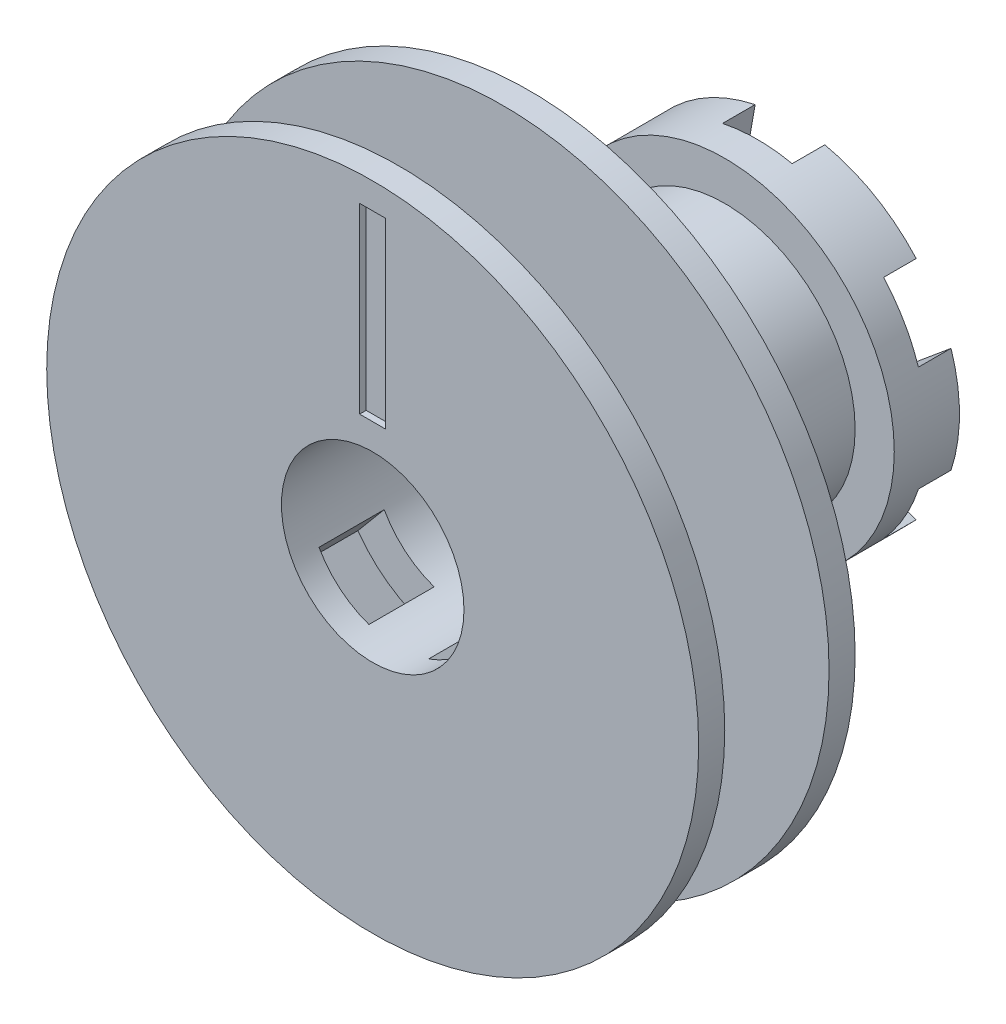
SolidWorks part; units mm, degrees
ref_plane "正面(Front)" through (0, 0, 0) normal (0, 0, 1) x (1, 0, 0)
ref_plane "平面(Top)" through (0, 0, 0) normal (0, 1, 0) x (1, 0, 0)
ref_plane "右側面(Right)" through (0, 0, 0) normal (1, 0, 0) x (0, 0, -1)
sketch "ｽｹｯﾁ1" plane through (0, 0, 0) normal (0, 0, 1) x (1, 0, 0)
  line L0 (0, 0) -> (0, 32.0386) construction
  line L1 (3.75, 6.4952) -> (2.4634, 13.9265)
  line L2 (0, 0) -> (3.75, 6.4952) construction
  arc A0 (2.4634, 13.9265) -> (0, 16) centre (0, 13.5) ccw
  dimension "D1" = 2.5
  dimension "D2" = 7.5
  dimension "D3" = 30
  dimension "D4" = 16
sketch "ｽｹｯﾁ2" plane through (0, 0, 0) normal (0, 0, 1) x (1, 0, 0)
  line L0 (3.75, 6.4952) -> (2.4634, 13.9265) construction
  line L1 (3.75, 6.4952) -> (2.4634, 13.9265)
  line L3 (0, 0) -> (0, 32.0386) construction
  line L4 (0, 0) -> (0, 32.0386) construction
  line L5 (-3.75, 6.4952) -> (-2.4634, 13.9265)
  line L6 (7.5, 0) -> (13.2924, 4.8299)
  line L7 (3.75, 6.4952) -> (10.829, 9.0966)
  line L8 (3.75, -6.4952) -> (10.829, -9.0966)
  line L9 (7.5, 0) -> (13.2924, -4.8299)
  line L10 (-3.75, -6.4952) -> (-2.4634, -13.9265)
  line L11 (3.75, -6.4952) -> (2.4634, -13.9265)
  line L12 (-7.5, 0) -> (-13.2924, -4.8299)
  line L13 (-3.75, -6.4952) -> (-10.829, -9.0966)
  line L14 (-3.75, 6.4952) -> (-10.829, 9.0966)
  line L15 (-7.5, 0) -> (-13.2924, 4.8299)
  line L16 (0, 0) -> (3.75, 6.4952) construction
  arc A0 (2.4634, 13.9265) -> (0, 16) centre (0, 13.5) ccw construction
  arc A1 (2.4634, 13.9265) -> (-2.4634, 13.9265) centre (0, 13.5) ccw
  arc A2 (13.2924, 4.8299) -> (10.829, 9.0966) centre (11.6913, 6.75) ccw
  arc A3 (10.829, -9.0966) -> (13.2924, -4.8299) centre (11.6913, -6.75) ccw
  arc A4 (-2.4634, -13.9265) -> (2.4634, -13.9265) centre (0, -13.5) ccw
  arc A5 (-13.2924, -4.8299) -> (-10.829, -9.0966) centre (-11.6913, -6.75) ccw
  arc A6 (-10.829, 9.0966) -> (-13.2924, 4.8299) centre (-11.6913, 6.75) ccw
  dimension "D2" = 7.5
  dimension "D3" = 30
  dimension "D1" = 6
sketch "ｽｹｯﾁ3" plane through (0, 0, 0) normal (0, 0, 1) x (1, 0, 0)
  circle A0 centre (0, 0) radius 13
  dimension "D1" = 26
extrude "ﾎﾞｽ - 押し出し1" add sketch "ｽｹｯﾁ3" along normal blind 5
extrude "ｶｯﾄ - 押し出し2" cut sketch "ｽｹｯﾁ2" along normal blind 2.5
sketch "ｽｹｯﾁ4" plane through (0, 0, 5) normal (0, 0, 1) x (1, 0, 0)
  circle A0 centre (0, 0) radius 10
  dimension "D1" = 20
sketch "ｽｹｯﾁ11" plane through (0, 0, 5) normal (0, 0, 1) x (1, 0, 0)
  circle A0 centre (0, 0) radius 10
  dimension "D1" = 20
extrude "ﾎﾞｽ - 押し出し2" add sketch "ｽｹｯﾁ11" along normal blind 15
sketch "ｽｹｯﾁ5" plane through (0, 0, 0) normal (0, 1, 0) x (1, 0, 0)
  line L0 (0, 0) -> (0, -21.9976) construction
  line L1 (0, -20) -> (25, -20)
  line L2 (-10, -20) -> (10, -20) construction
  line L3 (25, -20) -> (25, -22)
  line L4 (25, -22) -> (10, -22)
  line L5 (10, -22) -> (10, -30)
  line L6 (10, -30) -> (25, -30)
  line L7 (25, -30) -> (25, -32)
  line L8 (25, -32) -> (0, -32)
  line L9 (0, -20) -> (0, -32)
  dimension "D1" = 2
  dimension "D2" = 2
  dimension "D3" = 8
  dimension "D4" = 10
  dimension "D5" = 25
revolve "回転1" add sketch "ｽｹｯﾁ5" angle 360 about L0
sketch "ｽｹｯﾁ6" plane through (0, 0, 32) normal (0, 0, 1) x (1, 0, 0)
  circle A0 centre (0, 0) radius 2
  dimension "D1" = 4
extrude "ｶｯﾄ - 押し出し3" cut sketch "ｽｹｯﾁ6" against normal through all
sketch "ｽｹｯﾁ7" plane through (0, 0, 32) normal (0, 0, 1) x (1, 0, 0)
  circle A0 centre (0, 0) radius 7
  dimension "D1" = 14
extrude "ｶｯﾄ - 押し出し4" cut sketch "ｽｹｯﾁ7" against normal blind 23
sketch "ｽｹｯﾁ8" plane through (0, 0, 32) normal (0, 0, 1) x (1, 0, 0)
  line L0 (14.7902, 2.5) -> (9.6825, 2.5)
  line L1 (12.9904, 7.5) -> (6.6144, 7.5)
  line L2 (0, 0) -> (27.9307, 0) construction
  line L3 (14.7902, -2.5) -> (9.6825, -2.5)
  line L4 (12.9904, -7.5) -> (6.6144, -7.5)
  circle A0 centre (0, 0) radius 10 construction
  arc A1 (14.7902, 2.5) -> (12.9904, 7.5) centre (0, 0) ccw
  arc A2 (9.6825, 2.5) -> (6.6144, 7.5) centre (0, 0) ccw
  arc A3 (9.6825, -2.5) -> (6.6144, -7.5) centre (0, 0) cw
  arc A4 (14.7902, -2.5) -> (12.9904, -7.5) centre (0, 0) cw
  dimension "D1" = 20
  dimension "D4" = 5
  dimension "D2" = 5
  dimension "D3" = 5
extrude "ｶｯﾄ - 押し出し5" [suppressed] cut sketch "ｽｹｯﾁ8" against normal up to next contours A4 L3 A3 L4 | A2 L0 A1 L1
sketch "ｽｹｯﾁ9" plane through (0, 0, 30) normal (0, 0, -1) x (-1, 0, 0)
  line L0 (0, 0) -> (-20.5505, -24.4911) construction
  line L1 (0, 0) -> (0, -32.4809) construction
  line L2 (-3.8435, -0.6912) -> (-11.5569, -9.8837)
  line L3 (-3.8435, -0.6912) -> (-0.0133, -3.9051)
  line L4 (-11.5569, -9.8837) -> (-7.7267, -13.0976)
  line L5 (-0.0133, -3.9051) -> (-7.7267, -13.0976)
  line L6 (-3.8435, -0.6912) -> (-7.7267, -13.0976) construction
  line L7 (-11.5569, -9.8837) -> (-0.0133, -3.9051) construction
  point P5 (-5.7851, -6.8944)
  dimension "D1" = 40
  dimension "D2" = 5
  dimension "D3" = 12
  dimension "D4" = 3
extrude "ｶｯﾄ - 押し出し6" cut sketch "ｽｹｯﾁ9" along normal blind 5
mirror "ﾐﾗｰ1" about plane through (0, 0, 0) normal (1, 0, 0) of "ｶｯﾄ - 押し出し6"
fillet "ﾌｨﾚｯﾄ1" radius 1 2 edges at (4.3087, -9.0242, 27.5) (-4.3087, -9.0242, 27.5)
sketch "ｽｹｯﾁ10" plane through (0, 0, 32) normal (0, 0, 1) x (1, 0, 0)
  line L0 (0, 0) -> (0, 32.0386) construction
  line L1 (-1, 23) -> (1, 23)
  line L2 (-1, 23) -> (-1, 9)
  line L3 (-1, 9) -> (1, 9)
  line L4 (1, 23) -> (1, 9)
  line L5 (-1, 23) -> (1, 9) construction
  line L6 (-1, 9) -> (1, 23) construction
  circle A0 centre (0, 0) radius 25 construction
  circle A2 centre (0, 0) radius 7 construction
  point P0 (0, 16)
  dimension "D1" = 2
  dimension "D2" = 2
  dimension "D3" = 2
extrude "ｶｯﾄ - 押し出し7" cut sketch "ｽｹｯﾁ10" against normal blind 0.5
